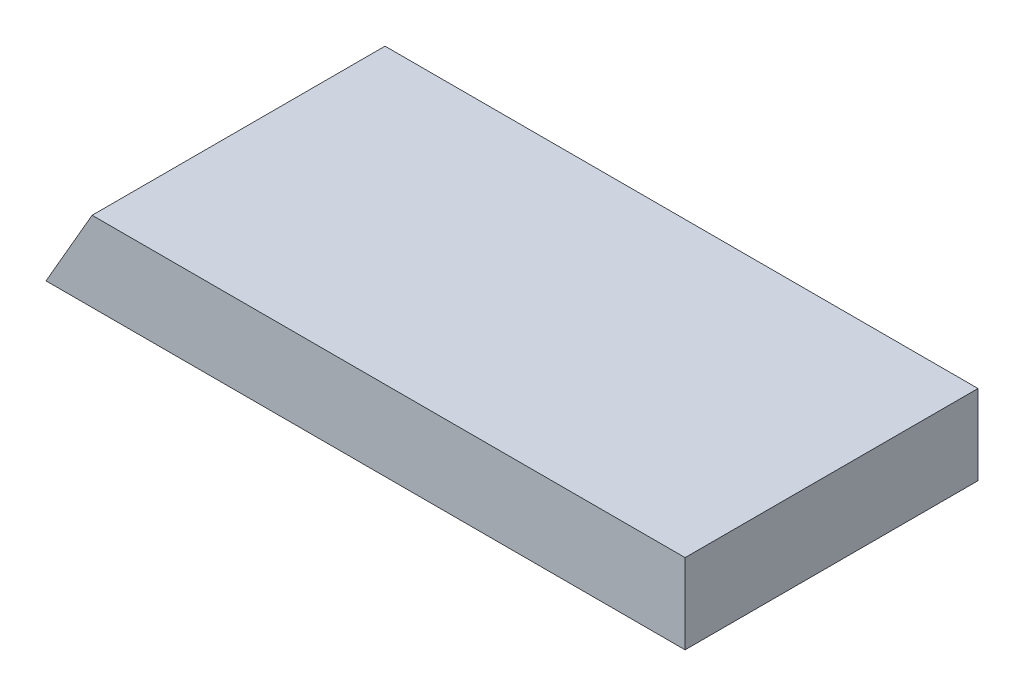
SolidWorks part; units mm, degrees
ref_plane "Front Plane" through (0, 0, 0) normal (0, 0, 1) x (1, 0, 0)
ref_plane "Top Plane" through (0, 0, 0) normal (0, 1, 0) x (1, 0, 0)
ref_plane "Right Plane" through (0, 0, 0) normal (1, 0, 0) x (0, 0, -1)
sketch "Sketch1" plane through (0, 0, 0) normal (0, 1, 0) x (1, 0, 0)
  line L1 (1.5673, 0) -> (306.3673, 0)
  line L2 (1.5673, 0) -> (1.5673, 139.7)
  line L3 (1.5673, 139.7) -> (306.3673, 139.7)
  line L4 (306.3673, 0) -> (306.3673, 139.7)
  dimension "D1" = 139.7
  dimension "D2" = 304.8
extrude "Boss-Extrude1" add sketch "Sketch1" along normal blind 38.1
sketch "Sketch2" plane through (0, 0, -139.7) normal (0, 0, -1) x (-1, 0, 0)
  line L0 (-1.5673, 0) -> (-23.5644, 38.1)
  line L1 (-306.3673, 38.1) -> (-1.5673, 38.1) construction
extrude "Cut-Extrude1" cut sketch "Sketch2" against normal through all and the other way through all flip side to cut
